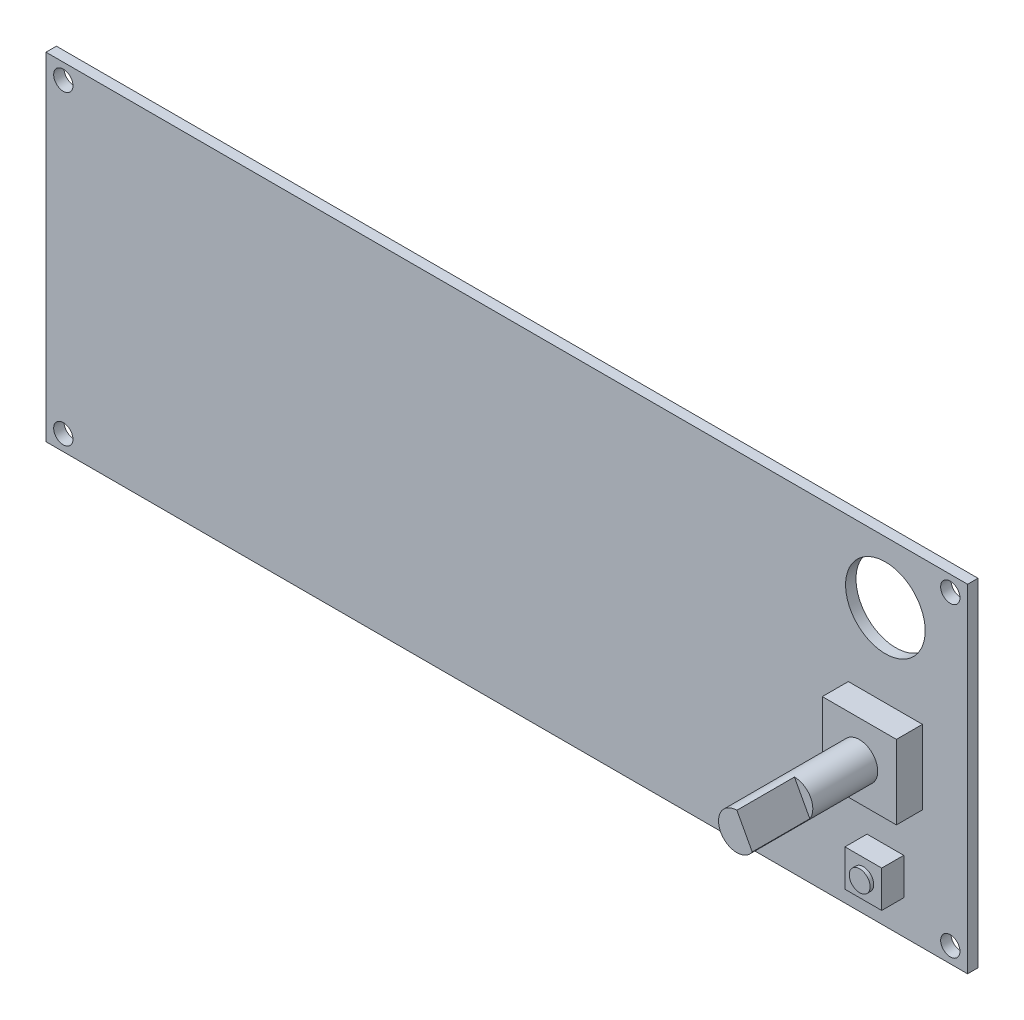
SolidWorks part; units mm, degrees
ref_plane "Front Plane" through (0, 0, 0) normal (0, 0, 1) x (1, 0, 0)
ref_plane "Top Plane" through (0, 0, 0) normal (0, 1, 0) x (1, 0, 0)
ref_plane "Right Plane" through (0, 0, 0) normal (1, 0, 0) x (0, 0, -1)
sketch "Sketch1" plane through (0, 0, 0) normal (0, 0, 1) x (1, 0, 0)
  line L1 (75.25, 27.55) -> (-75.25, 27.55)
  line L2 (75.25, 27.55) -> (75.25, -27.55)
  line L3 (75.25, -27.55) -> (-75.25, -27.55)
  line L4 (-75.25, 27.55) -> (-75.25, -27.55)
  line L5 (75.25, 27.55) -> (-75.25, -27.55) construction
  line L6 (75.25, -27.55) -> (-75.25, 27.55) construction
  line L7 (72.425, -25) -> (-72.425, -25) construction
  line L8 (72.425, -25) -> (72.425, 25) construction
  line L9 (72.425, 25) -> (-72.425, 25) construction
  line L10 (-72.425, -25) -> (-72.425, 25) construction
  line L11 (72.425, -25) -> (-72.425, 25) construction
  line L12 (72.425, 25) -> (-72.425, -25) construction
  line L13 (55.775, 4.05) -> (67.875, 4.05)
  line L14 (55.775, 4.05) -> (55.775, -8.05)
  line L15 (55.775, -8.05) -> (67.875, -8.05)
  line L16 (67.875, 4.05) -> (67.875, -8.05)
  line L17 (55.775, 4.05) -> (67.875, -8.05) construction
  line L18 (55.775, -8.05) -> (67.875, 4.05) construction
  line L19 (58.825, -16) -> (64.825, -16)
  line L20 (58.825, -16) -> (58.825, -22)
  line L21 (58.825, -22) -> (64.825, -22)
  line L22 (64.825, -16) -> (64.825, -22)
  line L23 (58.825, -16) -> (64.825, -22) construction
  line L24 (58.825, -22) -> (64.825, -16) construction
  circle A0 centre (-72.425, 25) radius 1.575
  circle A1 centre (72.425, 25) radius 1.575
  circle A2 centre (72.425, -25) radius 1.575
  circle A3 centre (-72.425, -25) radius 1.575
  circle A4 centre (61.825, 17.5) radius 6.5
  point P0 (0, 0)
  point P5 (0, 0)
  point P17 (61.825, -2)
  point P19 (61.825, -19)
  dimension "D3" = 3.15
  dimension "D6" = 27
  dimension "D7" = 13
  dimension "D1" = 55.1
  dimension "D2" = 150.5
  dimension "D4" = 144.85
  dimension "D5" = 50
  dimension "D8" = 19.5
  dimension "D9" = 17
  dimension "D10" = 6
  dimension "D11" = 12.1
  dimension "D12" = 10.6
extrude "Boss-Extrude1" add sketch "Sketch1" against normal blind 1.7
sketch "Sketch3" plane through (0, 0, 0) normal (0, 0, 1) x (1, 0, 0)
  line L1 (55.775, 4.05) -> (67.875, 4.05)
  line L2 (55.775, 4.05) -> (55.775, -8.05)
  line L3 (55.775, -8.05) -> (67.875, -8.05)
  line L4 (67.875, 4.05) -> (67.875, -8.05)
extrude "Boss-Extrude2" add sketch "Sketch3" along normal blind 4.25 and the other way up to surface (1.7 mm away) other way up to face at (61.825, -19, -1.7)
sketch "Sketch5" plane through (0, 0, 4.25) normal (0, 0, 1) x (1, 0, 0)
  line L0 (55.775, 4.05) -> (67.875, -8.05) construction
  circle A0 centre (61.825, -2) radius 3
  point P6 (61.825, -2)
  dimension "D1" = 6
extrude "Boss-Extrude3" add sketch "Sketch5" along normal blind 20
sketch "Sketch6" plane through (0, 0, 24.25) normal (0, 0, 1) x (1, 0, 0)
  line L0 (61.825, 1) -> (64.3332, -3.6459)
  line L1 (61.825, 1) -> (63.1233, 3.4232)
  line L2 (63.1233, 3.4232) -> (66.4845, -3.3185)
  line L3 (66.4845, -3.3185) -> (64.3332, -3.6459)
  circle A0 centre (61.825, -2) radius 3 construction
  circle A1 centre (61.825, -2) radius 3 construction
extrude "Cut-Extrude1" cut sketch "Sketch6" against normal blind 9.4
sketch "Sketch7" plane through (0, 0, 0) normal (0, 0, 1) x (1, 0, 0)
  line L1 (58.825, -16) -> (64.825, -16)
  line L2 (58.825, -16) -> (58.825, -22)
  line L3 (58.825, -22) -> (64.825, -22)
  line L4 (64.825, -16) -> (64.825, -22)
extrude "Boss-Extrude4" add sketch "Sketch7" along normal blind 3.6 and the other way up to surface (1.7 mm away) other way up to face at (61.825, -19, -1.7)
sketch "Sketch8" plane through (0, 0, 3.6) normal (0, 0, 1) x (1, 0, 0)
  line L0 (58.825, -16) -> (64.825, -22) construction
  circle A0 centre (61.825, -19) radius 1.7
  dimension "D1" = 3.4
extrude "Boss-Extrude5" add sketch "Sketch8" along normal blind 0.6
sketch "Sketch9" plane through (0, 0, -1.7) normal (0, 0, -1) x (-1, 0, 0)
  line L0 (75.25, 27.55) -> (75.25, -27.55) construction
  line L1 (75.25, 7.65) -> (48.85, 7.65)
  line L2 (75.25, 7.65) -> (75.25, -18.95)
  line L3 (75.25, -18.95) -> (48.85, -18.95)
  line L4 (48.85, 7.65) -> (48.85, -18.95)
  line L6 (75.25, -27.55) -> (-75.25, -27.55) construction
  dimension "D1" = 8.6
  dimension "D2" = 26.6
  dimension "D3" = 26.4
extrude "Boss-Extrude6" add sketch "Sketch9" along normal blind 2.75
sketch "Sketch10" plane through (0, 7.65, 0) normal (0, 1, 0) x (1, 0, 0)
  line L0 (-75.25, 4.45) -> (-75.25, 4.95)
  line L1 (-75.25, 4.95) -> (-73.05, 4.45)
  line L2 (-75.25, 4.45) -> (-48.85, 4.45) construction
  line L3 (-73.05, 4.45) -> (-75.25, 4.45)
  line L4 (-75.25, 1.7) -> (-48.85, 1.7) construction
  dimension "D1" = 3.25
  dimension "D2" = 2.2
extrude "Boss-Extrude7" add sketch "Sketch10" against normal up to surface (26.6 mm away) up to face at (-58.75, -18.95, -3.4187)
sketch "Sketch11" plane through (-75.25, 0, 0) normal (-1, 0, 0) x (0, 0, 1)
  line L0 (0, 27.55) -> (0, -27.55) construction
  line L1 (-4.2932, 6.9934) -> (-2.03, 6.9934)
  line L2 (-4.2932, 6.9934) -> (-4.2932, -18.2069)
  line L3 (-4.2932, -18.2069) -> (-2.03, -18.2069)
  line L4 (-2.03, 6.9934) -> (-2.03, -18.2069)
  dimension "D1" = 2.03
extrude "Cut-Extrude2" cut sketch "Sketch11" against normal blind 25.75
sketch "Sketch12" plane through (0, 0, -1.7) normal (0, 0, -1) x (-1, 0, 0)
  line L0 (75.25, -18.95) -> (75.25, -27.55) construction
  line L1 (-13.25, -2.7) -> (6.9818, -2.7)
  line L2 (-13.25, -2.7) -> (-13.25, -11.5)
  line L3 (-13.25, -11.5) -> (6.9818, -11.5)
  line L4 (30.25, -2.7) -> (30.25, -11.5)
  line L5 (-75.25, 27.55) -> (75.25, 27.55) construction
  line L6 (6.9818, -2.7) -> (6.9818, -11.5)
  line L7 (9.2945, -2.7) -> (9.2945, -11.5)
  line L8 (9.2945, -2.7) -> (30.25, -2.7)
  line L9 (9.2945, -11.5) -> (30.25, -11.5)
  dimension "D1" = 45
  dimension "D2" = 43.5
  dimension "D3" = 8.8
  dimension "D4" = 30.25
extrude "Boss-Extrude8" add sketch "Sketch12" along normal blind 9
sketch "Sketch13" plane through (0, -11.5, 0) normal (0, -1, 0) x (1, 0, 0)
  line L1 (12.355, -9.3331) -> (-5.3628, -9.3331)
  line L2 (12.355, -9.3331) -> (12.355, -2.8448)
  line L3 (12.355, -2.8448) -> (-5.3628, -2.8448)
  line L4 (-5.3628, -9.3331) -> (-5.3628, -2.8448)
  line L5 (-28.9614, -9.3331) -> (-10.0394, -9.3331)
  line L6 (-28.9614, -9.3331) -> (-28.9614, -2.8448)
  line L7 (-28.9614, -2.8448) -> (-10.0394, -2.8448)
  line L8 (-10.0394, -9.3331) -> (-10.0394, -2.8448)
extrude "Cut-Extrude3" cut sketch "Sketch13" against normal blind 8
